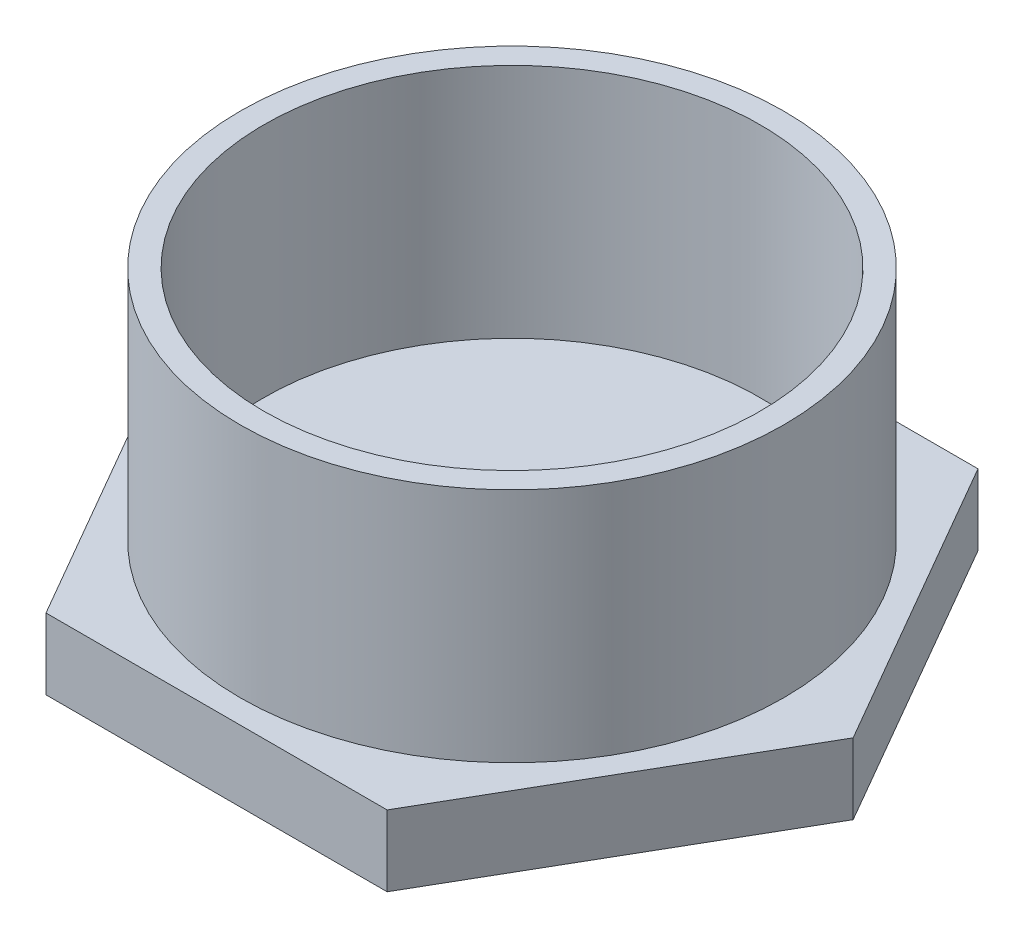
SolidWorks part; units mm, degrees
ref_plane "Front Plane" through (0, 0, 0) normal (0, 0, 1) x (1, 0, 0)
ref_plane "Top Plane" through (0, 0, 0) normal (0, 1, 0) x (1, 0, 0)
ref_plane "Right Plane" through (0, 0, 0) normal (1, 0, 0) x (0, 0, -1)
sketch "Sketch1" plane through (0, 0, 0) normal (0, 1, 0) x (1, 0, 0)
  line L1 (7.2169, -12.5) -> (14.4338, 0)
  line L2 (14.4338, 0) -> (7.2169, 12.5)
  line L3 (7.2169, 12.5) -> (-7.2169, 12.5)
  line L4 (-7.2169, 12.5) -> (-14.4338, 0)
  line L5 (-14.4338, 0) -> (-7.2169, -12.5)
  line L6 (-7.2169, -12.5) -> (7.2169, -12.5)
  circle A0 centre (0, 0) radius 12.5 construction
  dimension "D1" = 25
extrude "Boss-Extrude1" add sketch "Sketch1" along normal blind 3
sketch "Sketch2" plane through (0, 3, 0) normal (0, 1, 0) x (1, 0, 0)
  circle A0 centre (0, 0) radius 11.5
  dimension "D1" = 23
extrude "Boss-Extrude2" add sketch "Sketch2" along normal blind 10
sketch "Sketch3" plane through (0, 13, 0) normal (0, 1, 0) x (1, 0, 0)
  circle A0 centre (0, 0) radius 10.5
  dimension "D1" = 21
extrude "Cut-Extrude1" cut sketch "Sketch3" against normal blind 10
